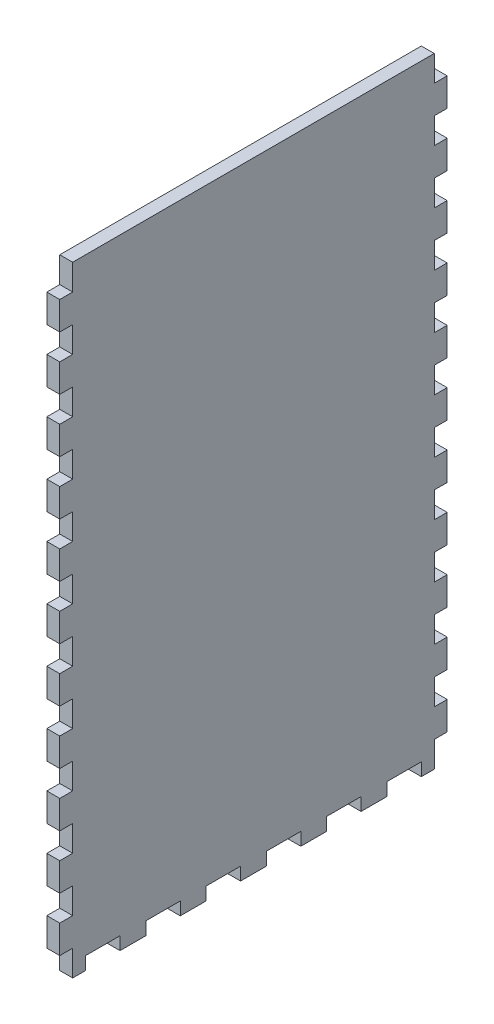
SolidWorks part; units mm, degrees
material "Acrylic (Medium-high impact)"
ref_plane "Front Plane" through (0, 0, 0) normal (0, 0, 1) x (1, 0, 0)
ref_plane "Top Plane" through (0, 0, 0) normal (0, 1, 0) x (1, 0, 0)
ref_plane "Right Plane" through (0, 0, 0) normal (1, 0, 0) x (0, 0, -1)
sketch "Sketch1" plane through (0, 0, 0) normal (0, 1, 0) x (1, 0, 0)
  line L1 (-254, 95.25) -> (254, 95.25)
  line L2 (-254, 95.25) -> (-254, -95.25)
  line L3 (-254, -95.25) -> (254, -95.25)
  line L4 (254, 95.25) -> (254, -95.25)
  point P4 (-254, 0)
  point P6 (0, 95.25)
  dimension "D1" = 190.5
  dimension "D2" = 508
extrude "Boss-Extrude1" add sketch "Sketch1" along normal blind 6.35
sketch "Sketch2" plane through (0, 6.35, 0) normal (0, 1, 0) x (1, 0, 0)
  line L0 (254, -95.25) -> (254, 95.25) construction
  line L1 (-254, 95.25) -> (254, 95.25)
  line L2 (-254, 95.25) -> (-254, -95.25)
  line L3 (-254, -95.25) -> (254, -95.25)
  line L4 (254, 95.25) -> (254, -95.25)
  line L5 (-254, -95.25) -> (254, -95.25) construction
  line L7 (-247.65, 88.9) -> (247.65, 88.9)
  line L8 (-247.65, 88.9) -> (-247.65, -88.9)
  line L9 (-247.65, -88.9) -> (247.65, -88.9)
  line L10 (247.65, 88.9) -> (247.65, -88.9)
  point P7 (-247.65, 0)
  point P14 (-254, 0)
  point P15 (0, -88.9)
  point P16 (0, -95.25)
  point P17 (247.65, 0)
  point P18 (254, 0)
  dimension "D1" = 6.35
  dimension "D2" = 6.35
extrude "Boss-Extrude2" add sketch "Sketch2" along normal blind 298.45
sketch "Sketch3" plane through (0, 0, 95.25) normal (0, 0, 1) x (1, 0, 0)
  line L0 (0, 304.8) -> (0, 0) construction
  line L1 (-254, 304.8) -> (254, 304.8) construction
  line L2 (-247.65, 6.35) -> (247.65, 6.35) construction
  line L4 (-3.302, 283.21) -> (-3.302, 6.35)
  line L5 (-3.302, 6.35) -> (3.302, 6.35)
  line L6 (3.302, 292.354) -> (3.302, 6.35)
  line L7 (3.302, 292.354) -> (-16.256, 292.354)
  line L9 (-5.842, 285.75) -> (-16.256, 285.75)
  line L10 (-16.256, 292.354) -> (-16.256, 285.75)
  line L11 (3.302, 101.6) -> (16.002, 101.6) construction
  line L12 (-254, 0) -> (254, 0) construction
  line L13 (12.827, 88.9) -> (12.827, 101.6) construction
  line L14 (9.652, 88.9) -> (16.002, 88.9)
  line L15 (9.652, 88.9) -> (9.652, 71.9667)
  line L16 (9.652, 71.9667) -> (16.002, 71.9667)
  line L17 (16.002, 88.9) -> (16.002, 71.9667)
  line L18 (9.652, 42.3333) -> (16.002, 42.3333)
  line L19 (9.652, 42.3333) -> (9.652, 59.2667)
  line L20 (9.652, 59.2667) -> (16.002, 59.2667)
  line L21 (16.002, 42.3333) -> (16.002, 59.2667)
  line L26 (9.652, 29.6333) -> (16.002, 29.6333)
  line L27 (9.652, 29.6333) -> (9.652, 12.7)
  line L28 (9.652, 12.7) -> (16.002, 12.7)
  line L29 (16.002, 29.6333) -> (16.002, 12.7)
  line L30 (12.827, 59.2667) -> (12.827, 71.9667) construction
  line L31 (12.827, 29.6333) -> (12.827, 42.3333) construction
  line L32 (12.827, 12.7) -> (12.827, 0) construction
  arc A0 (-3.302, 283.21) -> (-5.842, 285.75) centre (-5.842, 283.21) ccw
  point P5 (0, 6.35)
  dimension "D5" = 2.54
  dimension "D1" = 6.604
  dimension "D2" = 12.954
  dimension "D3" = 6.604
  dimension "D4" = 286.004
  dimension "D6" = 101.6
  dimension "D7" = 12.7
  dimension "D8" = 12.7
  dimension "D9" = 6.35
extrude "Cut-Extrude1" cut sketch "Sketch3" against normal blind 12.7
sketch "Sketch4" plane through (0, 0, -88.9) normal (0, 0, 1) x (1, 0, 0)
  line L0 (-254, 304.8) -> (254, 304.8) construction
  line L1 (-22.606, 304.8) -> (-16.256, 304.8)
  line L2 (-22.606, 304.8) -> (-22.606, 6.35)
  line L3 (-22.606, 6.35) -> (-16.256, 6.35)
  line L4 (-16.256, 304.8) -> (-16.256, 6.35)
  line L5 (6.477, 263.525) -> (6.477, 247.65) construction
  line L6 (-16.256, 292.354) -> (-16.256, 285.75) construction
  line L7 (3.302, 304.8) -> (9.652, 304.8)
  line L8 (3.302, 304.8) -> (3.302, 6.35)
  line L9 (3.302, 6.35) -> (9.652, 6.35)
  line L10 (9.652, 304.8) -> (9.652, 6.35)
  line L11 (247.65, 6.35) -> (-247.65, 6.35) construction
  line L12 (3.302, 6.35) -> (3.302, 292.354) construction
  line L13 (-16.256, 304.8) -> (-22.606, 304.8)
  line L14 (-16.256, 304.8) -> (-16.256, 292.1)
  line L15 (-16.256, 292.1) -> (-22.606, 292.1)
  line L16 (-22.606, 304.8) -> (-22.606, 292.1)
  line L17 (-16.256, 276.225) -> (-22.606, 276.225)
  line L18 (-16.256, 276.225) -> (-16.256, 263.525)
  line L19 (-16.256, 263.525) -> (-22.606, 263.525)
  line L20 (-22.606, 276.225) -> (-22.606, 263.525)
  line L21 (-22.606, 6.35) -> (-16.256, 6.35)
  line L22 (-22.606, 6.35) -> (-22.606, 19.05)
  line L23 (-22.606, 19.05) -> (-16.256, 19.05)
  line L24 (-16.256, 6.35) -> (-16.256, 19.05)
  line L25 (-22.606, 34.925) -> (-16.256, 34.925)
  line L26 (-22.606, 34.925) -> (-22.606, 47.625)
  line L27 (-22.606, 47.625) -> (-16.256, 47.625)
  line L28 (-16.256, 34.925) -> (-16.256, 47.625)
  line L29 (-22.606, 92.075) -> (-16.256, 92.075)
  line L30 (-22.606, 92.075) -> (-22.606, 104.775)
  line L31 (-22.606, 104.775) -> (-16.256, 104.775)
  line L32 (-16.256, 92.075) -> (-16.256, 104.775)
  line L33 (-22.606, 149.225) -> (-16.256, 149.225)
  line L34 (-22.606, 149.225) -> (-22.606, 161.925)
  line L35 (-22.606, 161.925) -> (-16.256, 161.925)
  line L36 (-16.256, 149.225) -> (-16.256, 161.925)
  line L37 (-22.606, 177.8) -> (-16.256, 177.8)
  line L38 (-22.606, 177.8) -> (-22.606, 190.5)
  line L39 (-22.606, 190.5) -> (-16.256, 190.5)
  line L40 (-16.256, 177.8) -> (-16.256, 190.5)
  line L41 (-22.606, 206.375) -> (-16.256, 206.375)
  line L42 (-22.606, 206.375) -> (-22.606, 219.075)
  line L43 (-22.606, 219.075) -> (-16.256, 219.075)
  line L44 (-16.256, 206.375) -> (-16.256, 219.075)
  line L45 (-22.606, 234.95) -> (-16.256, 234.95)
  line L46 (-22.606, 234.95) -> (-22.606, 247.65)
  line L47 (-22.606, 247.65) -> (-16.256, 247.65)
  line L48 (-16.256, 234.95) -> (-16.256, 247.65)
  line L49 (-16.256, 133.35) -> (-22.606, 133.35)
  line L50 (-16.256, 133.35) -> (-16.256, 120.65)
  line L51 (-16.256, 120.65) -> (-22.606, 120.65)
  line L52 (-22.606, 133.35) -> (-22.606, 120.65)
  line L53 (-16.256, 76.2) -> (-22.606, 76.2)
  line L54 (-16.256, 76.2) -> (-16.256, 63.5)
  line L55 (-16.256, 63.5) -> (-22.606, 63.5)
  line L56 (-22.606, 76.2) -> (-22.606, 63.5)
  line L57 (-19.431, 304.8) -> (-19.431, 292.1) construction
  line L58 (-19.431, 292.1) -> (-19.431, 276.225) construction
  line L59 (-19.431, 276.225) -> (-19.431, 263.525) construction
  line L60 (-19.431, 247.65) -> (-19.431, 234.95) construction
  line L61 (-19.431, 234.95) -> (-19.431, 219.075) construction
  line L62 (-19.431, 219.075) -> (-19.431, 206.375) construction
  line L63 (-19.431, 206.375) -> (-19.431, 190.5) construction
  line L64 (-19.431, 190.5) -> (-19.431, 177.8) construction
  line L65 (-19.431, 177.8) -> (-19.431, 161.925) construction
  line L66 (-19.431, 161.925) -> (-19.431, 149.225) construction
  line L67 (-19.431, 133.35) -> (-19.431, 120.65) construction
  line L68 (-19.431, 120.65) -> (-19.431, 104.775) construction
  line L69 (-19.431, 104.775) -> (-19.431, 92.075) construction
  line L70 (-19.431, 92.075) -> (-19.431, 76.2) construction
  line L71 (-19.431, 76.2) -> (-19.431, 63.5) construction
  line L72 (-19.431, 63.5) -> (-19.431, 47.625) construction
  line L73 (-19.431, 47.625) -> (-19.431, 34.925) construction
  line L74 (-19.431, 34.925) -> (-19.431, 19.05) construction
  line L75 (-19.431, 19.05) -> (-19.431, 6.35) construction
  line L76 (-19.431, 149.225) -> (-19.431, 133.35) construction
  line L77 (-19.431, 263.525) -> (-19.431, 247.65) construction
  line L78 (-6.477, 304.8) -> (-6.477, 0) construction
  line L79 (254, 304.8) -> (-254, 304.8) construction
  line L80 (254, 0) -> (-254, 0) construction
  line L81 (-6.477, 8.3493) -> (3.302, 8.3493) construction
  line L82 (-6.477, 8.3493) -> (-16.256, 8.3493) construction
  line L83 (6.477, 149.225) -> (6.477, 133.35) construction
  line L84 (6.477, 19.05) -> (6.477, 6.35) construction
  line L85 (6.477, 34.925) -> (6.477, 19.05) construction
  line L86 (6.477, 47.625) -> (6.477, 34.925) construction
  line L87 (6.477, 63.5) -> (6.477, 47.625) construction
  line L88 (6.477, 76.2) -> (6.477, 63.5) construction
  line L89 (6.477, 92.075) -> (6.477, 76.2) construction
  line L90 (6.477, 104.775) -> (6.477, 92.075) construction
  line L91 (6.477, 120.65) -> (6.477, 104.775) construction
  line L92 (6.477, 133.35) -> (6.477, 120.65) construction
  line L93 (6.477, 161.925) -> (6.477, 149.225) construction
  line L94 (6.477, 177.8) -> (6.477, 161.925) construction
  line L95 (6.477, 190.5) -> (6.477, 177.8) construction
  line L96 (6.477, 206.375) -> (6.477, 190.5) construction
  line L97 (6.477, 219.075) -> (6.477, 206.375) construction
  line L98 (6.477, 234.95) -> (6.477, 219.075) construction
  line L99 (6.477, 247.65) -> (6.477, 234.95) construction
  line L100 (6.477, 276.225) -> (6.477, 263.525) construction
  line L101 (6.477, 292.1) -> (6.477, 276.225) construction
  line L102 (6.477, 304.8) -> (6.477, 292.1) construction
  line L103 (9.652, 76.2) -> (9.652, 63.5)
  line L104 (3.302, 63.5) -> (9.652, 63.5)
  line L105 (3.302, 76.2) -> (3.302, 63.5)
  line L106 (3.302, 76.2) -> (9.652, 76.2)
  line L107 (9.652, 133.35) -> (9.652, 120.65)
  line L108 (3.302, 120.65) -> (9.652, 120.65)
  line L109 (3.302, 133.35) -> (3.302, 120.65)
  line L110 (3.302, 133.35) -> (9.652, 133.35)
  line L111 (3.302, 234.95) -> (3.302, 247.65)
  line L112 (9.652, 247.65) -> (3.302, 247.65)
  line L113 (9.652, 234.95) -> (9.652, 247.65)
  line L114 (9.652, 234.95) -> (3.302, 234.95)
  line L115 (3.302, 206.375) -> (3.302, 219.075)
  line L116 (9.652, 219.075) -> (3.302, 219.075)
  line L117 (9.652, 206.375) -> (9.652, 219.075)
  line L118 (9.652, 206.375) -> (3.302, 206.375)
  line L119 (3.302, 177.8) -> (3.302, 190.5)
  line L120 (9.652, 190.5) -> (3.302, 190.5)
  line L121 (9.652, 177.8) -> (9.652, 190.5)
  line L122 (9.652, 177.8) -> (3.302, 177.8)
  line L123 (3.302, 149.225) -> (3.302, 161.925)
  line L124 (9.652, 161.925) -> (3.302, 161.925)
  line L125 (9.652, 149.225) -> (9.652, 161.925)
  line L126 (9.652, 149.225) -> (3.302, 149.225)
  line L127 (3.302, 92.075) -> (3.302, 104.775)
  line L128 (9.652, 104.775) -> (3.302, 104.775)
  line L129 (9.652, 92.075) -> (9.652, 104.775)
  line L130 (9.652, 92.075) -> (3.302, 92.075)
  line L131 (3.302, 34.925) -> (3.302, 47.625)
  line L132 (9.652, 47.625) -> (3.302, 47.625)
  line L133 (9.652, 34.925) -> (9.652, 47.625)
  line L134 (9.652, 34.925) -> (3.302, 34.925)
  line L135 (3.302, 6.35) -> (3.302, 19.05)
  line L136 (9.652, 19.05) -> (3.302, 19.05)
  line L137 (9.652, 6.35) -> (9.652, 19.05)
  line L138 (9.652, 6.35) -> (3.302, 6.35)
  line L139 (9.652, 276.225) -> (9.652, 263.525)
  line L140 (3.302, 263.525) -> (9.652, 263.525)
  line L141 (3.302, 276.225) -> (3.302, 263.525)
  line L142 (3.302, 276.225) -> (9.652, 276.225)
  line L143 (9.652, 304.8) -> (9.652, 292.1)
  line L144 (3.302, 292.1) -> (9.652, 292.1)
  line L145 (3.302, 304.8) -> (3.302, 292.1)
  line L146 (3.302, 304.8) -> (9.652, 304.8)
  line L147 (3.302, 304.8) -> (3.302, 6.35)
  line L148 (9.652, 6.35) -> (3.302, 6.35)
  line L149 (9.652, 304.8) -> (9.652, 6.35)
  line L150 (9.652, 304.8) -> (3.302, 304.8)
  point P14 (-16.256, 289.052)
  dimension "D1" = 6.35
  dimension "D2" = 12.7
extrude "Cut-Extrude2" cut sketch "Sketch4" against normal up to next (6.35 mm away) contours L17 L4 L15 L2 | L2 L47 L4 L19 | L45 L2 L43 L4 | L41 L2 L39 L4 | L37 L2 L35 L4 | L49 L4 L33 L2 | L4 L51 L2 L31 | L53 L4 L29 L2 | L4 L55 L2 L27 | L25 L2 L23 L4
ref_plane "Plane1" through (-6.477, 0, 0) normal (-1, 0, 0) x (0, 0, 1)
mirror "Mirror1" about plane through (-6.477, 0, 0) normal (-1, 0, 0) of "Cut-Extrude2"
sketch "Sketch5" plane through (0, 0, 0) normal (0, -1, 0) x (-1, 0, 0)
  line L0 (-227.9316, -95.25) -> (-227.9316, -88.9)
  line L1 (-247.65, 88.9) -> (247.65, 88.9)
  line L2 (-247.65, 88.9) -> (-247.65, -88.9)
  line L3 (-247.65, -88.9) -> (247.65, -88.9)
  line L4 (247.65, 88.9) -> (247.65, -88.9)
  line L5 (-254, -95.25) -> (-241.3, -95.25)
  line L6 (-254, -95.25) -> (-254, -88.9)
  line L7 (-254, -88.9) -> (-241.3, -88.9)
  line L8 (-241.3, -95.25) -> (-241.3, -88.9)
  line L9 (-227.9316, -95.25) -> (-215.2316, -95.25)
  line L10 (-227.9316, -88.9) -> (-215.2316, -88.9)
  line L11 (-215.2316, -95.25) -> (-215.2316, -88.9)
  line L12 (-201.8632, -95.25) -> (-201.8632, -88.9)
  line L13 (-201.8632, -95.25) -> (-189.1632, -95.25)
  line L14 (-201.8632, -88.9) -> (-189.1632, -88.9)
  line L15 (-189.1632, -95.25) -> (-189.1632, -88.9)
  line L16 (-175.7947, -95.25) -> (-175.7947, -88.9)
  line L17 (-175.7947, -95.25) -> (-163.0947, -95.25)
  line L18 (-175.7947, -88.9) -> (-163.0947, -88.9)
  line L19 (-163.0947, -95.25) -> (-163.0947, -88.9)
  line L20 (-149.7263, -95.25) -> (-149.7263, -88.9)
  line L21 (-149.7263, -95.25) -> (-137.0263, -95.25)
  line L22 (-149.7263, -88.9) -> (-137.0263, -88.9)
  line L23 (-137.0263, -95.25) -> (-137.0263, -88.9)
  line L24 (-123.6579, -95.25) -> (-123.6579, -88.9)
  line L25 (-123.6579, -95.25) -> (-110.9579, -95.25)
  line L26 (-123.6579, -88.9) -> (-110.9579, -88.9)
  line L27 (-110.9579, -95.25) -> (-110.9579, -88.9)
  line L28 (-97.5895, -95.25) -> (-97.5895, -88.9)
  line L29 (-97.5895, -95.25) -> (-84.8895, -95.25)
  line L30 (-97.5895, -88.9) -> (-84.8895, -88.9)
  line L31 (-84.8895, -95.25) -> (-84.8895, -88.9)
  line L32 (-71.5211, -95.25) -> (-71.5211, -88.9)
  line L33 (-71.5211, -95.25) -> (-58.8211, -95.25)
  line L34 (-71.5211, -88.9) -> (-58.8211, -88.9)
  line L35 (-58.8211, -95.25) -> (-58.8211, -88.9)
  line L36 (-45.4526, -95.25) -> (-45.4526, -88.9)
  line L37 (-45.4526, -95.25) -> (-32.7526, -95.25)
  line L38 (-45.4526, -88.9) -> (-32.7526, -88.9)
  line L39 (-32.7526, -95.25) -> (-32.7526, -88.9)
  line L40 (-19.3842, -95.25) -> (-19.3842, -88.9)
  line L41 (-19.3842, -95.25) -> (-6.6842, -95.25)
  line L42 (-19.3842, -88.9) -> (-6.6842, -88.9)
  line L43 (-6.6842, -95.25) -> (-6.6842, -88.9)
  line L44 (6.6842, -95.25) -> (6.6842, -88.9)
  line L45 (6.6842, -95.25) -> (19.3842, -95.25)
  line L46 (6.6842, -88.9) -> (19.3842, -88.9)
  line L47 (19.3842, -95.25) -> (19.3842, -88.9)
  line L48 (32.7526, -95.25) -> (32.7526, -88.9)
  line L49 (32.7526, -95.25) -> (45.4526, -95.25)
  line L50 (32.7526, -88.9) -> (45.4526, -88.9)
  line L51 (45.4526, -95.25) -> (45.4526, -88.9)
  line L52 (58.8211, -95.25) -> (58.8211, -88.9)
  line L53 (58.8211, -95.25) -> (71.5211, -95.25)
  line L54 (58.8211, -88.9) -> (71.5211, -88.9)
  line L55 (71.5211, -95.25) -> (71.5211, -88.9)
  line L56 (84.8895, -95.25) -> (84.8895, -88.9)
  line L57 (84.8895, -95.25) -> (97.5895, -95.25)
  line L58 (84.8895, -88.9) -> (97.5895, -88.9)
  line L59 (97.5895, -95.25) -> (97.5895, -88.9)
  line L60 (110.9579, -95.25) -> (110.9579, -88.9)
  line L61 (110.9579, -95.25) -> (123.6579, -95.25)
  line L62 (110.9579, -88.9) -> (123.6579, -88.9)
  line L63 (123.6579, -95.25) -> (123.6579, -88.9)
  line L64 (137.0263, -95.25) -> (137.0263, -88.9)
  line L65 (137.0263, -95.25) -> (149.7263, -95.25)
  line L66 (137.0263, -88.9) -> (149.7263, -88.9)
  line L67 (149.7263, -95.25) -> (149.7263, -88.9)
  line L68 (163.0947, -95.25) -> (163.0947, -88.9)
  line L69 (163.0947, -95.25) -> (175.7947, -95.25)
  line L70 (163.0947, -88.9) -> (175.7947, -88.9)
  line L71 (175.7947, -95.25) -> (175.7947, -88.9)
  line L72 (189.1632, -95.25) -> (189.1632, -88.9)
  line L73 (189.1632, -95.25) -> (201.8632, -95.25)
  line L74 (189.1632, -88.9) -> (201.8632, -88.9)
  line L75 (201.8632, -95.25) -> (201.8632, -88.9)
  line L76 (215.2316, -95.25) -> (215.2316, -88.9)
  line L77 (215.2316, -95.25) -> (227.9316, -95.25)
  line L78 (215.2316, -88.9) -> (227.9316, -88.9)
  line L79 (227.9316, -95.25) -> (227.9316, -88.9)
  line L80 (241.3, -95.25) -> (241.3, -88.9)
  line L81 (241.3, -95.25) -> (254, -95.25)
  line L82 (241.3, -88.9) -> (254, -88.9)
  line L83 (254, -95.25) -> (254, -88.9)
  line L84 (-167.64, 0) -> (167.64, 0) construction
  line L85 (254, 95.25) -> (254, 88.9)
  line L86 (241.3, 88.9) -> (254, 88.9)
  line L87 (241.3, 95.25) -> (254, 95.25)
  line L88 (241.3, 95.25) -> (241.3, 88.9)
  line L89 (227.9316, 95.25) -> (227.9316, 88.9)
  line L90 (215.2316, 88.9) -> (227.9316, 88.9)
  line L91 (215.2316, 95.25) -> (227.9316, 95.25)
  line L92 (215.2316, 95.25) -> (215.2316, 88.9)
  line L93 (201.8632, 95.25) -> (201.8632, 88.9)
  line L94 (189.1632, 88.9) -> (201.8632, 88.9)
  line L95 (189.1632, 95.25) -> (201.8632, 95.25)
  line L96 (189.1632, 95.25) -> (189.1632, 88.9)
  line L97 (175.7947, 95.25) -> (175.7947, 88.9)
  line L98 (163.0947, 88.9) -> (175.7947, 88.9)
  line L99 (163.0947, 95.25) -> (175.7947, 95.25)
  line L100 (163.0947, 95.25) -> (163.0947, 88.9)
  line L101 (149.7263, 95.25) -> (149.7263, 88.9)
  line L102 (137.0263, 88.9) -> (149.7263, 88.9)
  line L103 (137.0263, 95.25) -> (149.7263, 95.25)
  line L104 (137.0263, 95.25) -> (137.0263, 88.9)
  line L105 (123.6579, 95.25) -> (123.6579, 88.9)
  line L106 (110.9579, 88.9) -> (123.6579, 88.9)
  line L107 (110.9579, 95.25) -> (123.6579, 95.25)
  line L108 (110.9579, 95.25) -> (110.9579, 88.9)
  line L109 (97.5895, 95.25) -> (97.5895, 88.9)
  line L110 (84.8895, 88.9) -> (97.5895, 88.9)
  line L111 (84.8895, 95.25) -> (97.5895, 95.25)
  line L112 (84.8895, 95.25) -> (84.8895, 88.9)
  line L113 (71.5211, 95.25) -> (71.5211, 88.9)
  line L114 (58.8211, 88.9) -> (71.5211, 88.9)
  line L115 (58.8211, 95.25) -> (71.5211, 95.25)
  line L116 (58.8211, 95.25) -> (58.8211, 88.9)
  line L117 (45.4526, 95.25) -> (45.4526, 88.9)
  line L118 (32.7526, 88.9) -> (45.4526, 88.9)
  line L119 (32.7526, 95.25) -> (45.4526, 95.25)
  line L120 (32.7526, 95.25) -> (32.7526, 88.9)
  line L121 (19.3842, 95.25) -> (19.3842, 88.9)
  line L122 (6.6842, 88.9) -> (19.3842, 88.9)
  line L123 (6.6842, 95.25) -> (19.3842, 95.25)
  line L124 (6.6842, 95.25) -> (6.6842, 88.9)
  line L125 (-6.6842, 95.25) -> (-6.6842, 88.9)
  line L126 (-19.3842, 88.9) -> (-6.6842, 88.9)
  line L127 (-19.3842, 95.25) -> (-6.6842, 95.25)
  line L128 (-19.3842, 95.25) -> (-19.3842, 88.9)
  line L129 (-32.7526, 95.25) -> (-32.7526, 88.9)
  line L130 (-45.4526, 88.9) -> (-32.7526, 88.9)
  line L131 (-45.4526, 95.25) -> (-32.7526, 95.25)
  line L132 (-45.4526, 95.25) -> (-45.4526, 88.9)
  line L133 (-58.8211, 95.25) -> (-58.8211, 88.9)
  line L134 (-71.5211, 88.9) -> (-58.8211, 88.9)
  line L135 (-71.5211, 95.25) -> (-58.8211, 95.25)
  line L136 (-71.5211, 95.25) -> (-71.5211, 88.9)
  line L137 (-84.8895, 95.25) -> (-84.8895, 88.9)
  line L138 (-97.5895, 88.9) -> (-84.8895, 88.9)
  line L139 (-97.5895, 95.25) -> (-84.8895, 95.25)
  line L140 (-97.5895, 95.25) -> (-97.5895, 88.9)
  line L141 (-110.9579, 95.25) -> (-110.9579, 88.9)
  line L142 (-123.6579, 88.9) -> (-110.9579, 88.9)
  line L143 (-123.6579, 95.25) -> (-110.9579, 95.25)
  line L144 (-123.6579, 95.25) -> (-123.6579, 88.9)
  line L145 (-137.0263, 95.25) -> (-137.0263, 88.9)
  line L146 (-149.7263, 88.9) -> (-137.0263, 88.9)
  line L147 (-149.7263, 95.25) -> (-137.0263, 95.25)
  line L148 (-149.7263, 95.25) -> (-149.7263, 88.9)
  line L149 (-163.0947, 95.25) -> (-163.0947, 88.9)
  line L150 (-175.7947, 88.9) -> (-163.0947, 88.9)
  line L151 (-175.7947, 95.25) -> (-163.0947, 95.25)
  line L152 (-175.7947, 95.25) -> (-175.7947, 88.9)
  line L153 (-189.1632, 95.25) -> (-189.1632, 88.9)
  line L154 (-201.8632, 88.9) -> (-189.1632, 88.9)
  line L155 (-201.8632, 95.25) -> (-189.1632, 95.25)
  line L156 (-201.8632, 95.25) -> (-201.8632, 88.9)
  line L157 (-215.2316, 95.25) -> (-215.2316, 88.9)
  line L158 (-227.9316, 88.9) -> (-215.2316, 88.9)
  line L159 (-227.9316, 95.25) -> (-215.2316, 95.25)
  line L160 (-241.3, 95.25) -> (-241.3, 88.9)
  line L161 (-254, 88.9) -> (-241.3, 88.9)
  line L162 (-254, 95.25) -> (-254, 88.9)
  line L163 (-254, 95.25) -> (-241.3, 95.25)
  line L164 (-247.65, 88.9) -> (247.65, 88.9)
  line L165 (-227.9316, 95.25) -> (-227.9316, 88.9)
  line L166 (-254, 65.6167) -> (-254, 52.9167)
  line L167 (-254, 95.25) -> (-247.65, 95.25)
  line L168 (-254, 95.25) -> (-254, 82.55)
  line L169 (-254, 82.55) -> (-247.65, 82.55)
  line L170 (-247.65, 95.25) -> (-247.65, 82.55)
  line L171 (-254, 65.6167) -> (-247.65, 65.6167)
  line L172 (-247.65, 65.6167) -> (-247.65, 52.9167)
  line L173 (-254, 52.9167) -> (-247.65, 52.9167)
  line L174 (-254, 35.9833) -> (-254, 23.2833)
  line L175 (-254, 35.9833) -> (-247.65, 35.9833)
  line L176 (-247.65, 35.9833) -> (-247.65, 23.2833)
  line L177 (-254, 23.2833) -> (-247.65, 23.2833)
  line L178 (-254, 6.35) -> (-254, -6.35)
  line L179 (-254, 6.35) -> (-247.65, 6.35)
  line L180 (-247.65, 6.35) -> (-247.65, -6.35)
  line L181 (-254, -6.35) -> (-247.65, -6.35)
  line L182 (-254, -23.2833) -> (-254, -35.9833)
  line L183 (-254, -23.2833) -> (-247.65, -23.2833)
  line L184 (-247.65, -23.2833) -> (-247.65, -35.9833)
  line L185 (-254, -35.9833) -> (-247.65, -35.9833)
  line L186 (-254, -52.9167) -> (-254, -65.6167)
  line L187 (-254, -52.9167) -> (-247.65, -52.9167)
  line L188 (-247.65, -52.9167) -> (-247.65, -65.6167)
  line L189 (-254, -65.6167) -> (-247.65, -65.6167)
  line L190 (-254, -82.55) -> (-254, -95.25)
  line L191 (-254, -82.55) -> (-247.65, -82.55)
  line L192 (-247.65, -82.55) -> (-247.65, -95.25)
  line L193 (-254, -95.25) -> (-247.65, -95.25)
  line L194 (0, 104.775) -> (0, -104.775) construction
  line L195 (254, -95.25) -> (247.65, -95.25)
  line L196 (247.65, -82.55) -> (247.65, -95.25)
  line L197 (254, -82.55) -> (247.65, -82.55)
  line L198 (254, -82.55) -> (254, -95.25)
  line L199 (254, -65.6167) -> (247.65, -65.6167)
  line L200 (247.65, -52.9167) -> (247.65, -65.6167)
  line L201 (254, -52.9167) -> (247.65, -52.9167)
  line L202 (254, -52.9167) -> (254, -65.6167)
  line L203 (254, -35.9833) -> (247.65, -35.9833)
  line L204 (247.65, -23.2833) -> (247.65, -35.9833)
  line L205 (254, -23.2833) -> (247.65, -23.2833)
  line L206 (254, -23.2833) -> (254, -35.9833)
  line L207 (254, -6.35) -> (247.65, -6.35)
  line L208 (247.65, 6.35) -> (247.65, -6.35)
  line L209 (254, 6.35) -> (247.65, 6.35)
  line L210 (254, 6.35) -> (254, -6.35)
  line L211 (254, 23.2833) -> (247.65, 23.2833)
  line L212 (247.65, 35.9833) -> (247.65, 23.2833)
  line L213 (254, 35.9833) -> (247.65, 35.9833)
  line L214 (254, 35.9833) -> (254, 23.2833)
  line L215 (254, 52.9167) -> (247.65, 52.9167)
  line L216 (247.65, 65.6167) -> (247.65, 52.9167)
  line L217 (254, 65.6167) -> (247.65, 65.6167)
  line L218 (247.65, 95.25) -> (247.65, 82.55)
  line L219 (254, 82.55) -> (247.65, 82.55)
  line L220 (254, 95.25) -> (254, 82.55)
  line L221 (254, 95.25) -> (247.65, 95.25)
  line L222 (254, 65.6167) -> (254, 52.9167)
  line L223 (254, 95.25) -> (254, 88.9)
  line L224 (254, -95.25) -> (254, -88.9)
  line L225 (247.65, 88.9) -> (247.65, -88.9)
  line M114 (254, -95.25) -> (254, 95.25)
  dimension "D1" = 12.7
  dimension "D3" = 6.35
  dimension "D5" = 12.7
  dimension "D2" = 20
  dimension "D4" = 7
sketch "Sketch6" plane through (0, 0, 0) normal (0, 1, 0) x (1, 0, 0)
  line L1 (-247.65, 117.4399) -> (267.1511, 117.4399)
  line L2 (-247.65, 117.4399) -> (-247.65, -137.4416)
  line L3 (-247.65, -137.4416) -> (267.1511, -137.4416)
  line L4 (267.1511, 117.4399) -> (267.1511, -137.4416)
  line L6 (-247.65, 88.9) -> (-247.65, -88.9) construction
  point P4 (-247.65, 144.2667)
  point P5 (-247.65, -168.1175)
extrude "Cut-Extrude5" cut sketch "Sketch6" along normal through all
extrude "Cut-Extrude6" cut sketch "Sketch5" against normal blind 6.35 contours L199 L4 L197 M114 | L203 L4 L201 M114 | L207 L4 L205 M114 | L211 L4 L209 M114 | L215 L4 L213 M114 | L219 L4 L217 M114
sketch "Sketch7" plane through (-254, 0, 0) normal (-1, 0, 0) x (0, 0, 1)
  line L0 (-95.25, 26.5545) -> (-95.25, 39.2545)
  line L1 (-95.25, 0) -> (-88.9, 0)
  line L2 (-95.25, 0) -> (-95.25, 12.7)
  line L3 (-95.25, 12.7) -> (-88.9, 12.7)
  line L4 (-88.9, 0) -> (-88.9, 12.7)
  line L5 (-95.25, 39.2545) -> (-88.9, 39.2545)
  line L6 (-88.9, 26.5545) -> (-88.9, 39.2545)
  line L7 (-95.25, 26.5545) -> (-88.9, 26.5545)
  line L8 (-95.25, 53.1091) -> (-95.25, 65.8091)
  line L9 (-95.25, 65.8091) -> (-88.9, 65.8091)
  line L10 (-88.9, 53.1091) -> (-88.9, 65.8091)
  line L11 (-95.25, 53.1091) -> (-88.9, 53.1091)
  line L12 (-95.25, 79.6636) -> (-95.25, 92.3636)
  line L13 (-95.25, 92.3636) -> (-88.9, 92.3636)
  line L14 (-88.9, 79.6636) -> (-88.9, 92.3636)
  line L15 (-95.25, 79.6636) -> (-88.9, 79.6636)
  line L16 (-95.25, 106.2182) -> (-95.25, 118.9182)
  line L17 (-95.25, 118.9182) -> (-88.9, 118.9182)
  line L18 (-88.9, 106.2182) -> (-88.9, 118.9182)
  line L19 (-95.25, 106.2182) -> (-88.9, 106.2182)
  line L20 (-95.25, 132.7727) -> (-95.25, 145.4727)
  line L21 (-95.25, 145.4727) -> (-88.9, 145.4727)
  line L22 (-88.9, 132.7727) -> (-88.9, 145.4727)
  line L23 (-95.25, 132.7727) -> (-88.9, 132.7727)
  line L24 (-95.25, 159.3273) -> (-95.25, 172.0273)
  line L25 (-95.25, 172.0273) -> (-88.9, 172.0273)
  line L26 (-88.9, 159.3273) -> (-88.9, 172.0273)
  line L27 (-95.25, 159.3273) -> (-88.9, 159.3273)
  line L28 (-95.25, 185.8818) -> (-95.25, 198.5818)
  line L29 (-95.25, 198.5818) -> (-88.9, 198.5818)
  line L30 (-88.9, 185.8818) -> (-88.9, 198.5818)
  line L31 (-95.25, 185.8818) -> (-88.9, 185.8818)
  line L32 (-95.25, 212.4364) -> (-95.25, 225.1364)
  line L33 (-95.25, 225.1364) -> (-88.9, 225.1364)
  line L34 (-88.9, 212.4364) -> (-88.9, 225.1364)
  line L35 (-95.25, 212.4364) -> (-88.9, 212.4364)
  line L36 (-95.25, 238.9909) -> (-95.25, 251.6909)
  line L37 (-95.25, 251.6909) -> (-88.9, 251.6909)
  line L38 (-88.9, 238.9909) -> (-88.9, 251.6909)
  line L39 (-95.25, 238.9909) -> (-88.9, 238.9909)
  line L40 (-95.25, 265.5455) -> (-95.25, 278.2455)
  line L41 (-95.25, 278.2455) -> (-88.9, 278.2455)
  line L42 (-88.9, 265.5455) -> (-88.9, 278.2455)
  line L43 (-95.25, 265.5455) -> (-88.9, 265.5455)
  line L44 (-95.25, 292.1) -> (-95.25, 304.8)
  line L45 (-95.25, 304.8) -> (-88.9, 304.8)
  line L46 (-88.9, 292.1) -> (-88.9, 304.8)
  line L47 (-95.25, 292.1) -> (-88.9, 292.1)
  line L48 (0, -3.4925) -> (0, 3.4925) construction
  line L49 (95.25, 292.1) -> (88.9, 292.1)
  line L50 (88.9, 292.1) -> (88.9, 304.8)
  line L51 (95.25, 304.8) -> (88.9, 304.8)
  line L52 (95.25, 292.1) -> (95.25, 304.8)
  line L53 (95.25, 265.5455) -> (88.9, 265.5455)
  line L54 (88.9, 265.5455) -> (88.9, 278.2455)
  line L55 (95.25, 278.2455) -> (88.9, 278.2455)
  line L56 (95.25, 265.5455) -> (95.25, 278.2455)
  line L57 (95.25, 238.9909) -> (88.9, 238.9909)
  line L58 (88.9, 238.9909) -> (88.9, 251.6909)
  line L59 (95.25, 251.6909) -> (88.9, 251.6909)
  line L60 (95.25, 238.9909) -> (95.25, 251.6909)
  line L61 (95.25, 212.4364) -> (88.9, 212.4364)
  line L62 (88.9, 212.4364) -> (88.9, 225.1364)
  line L63 (95.25, 225.1364) -> (88.9, 225.1364)
  line L64 (95.25, 212.4364) -> (95.25, 225.1364)
  line L65 (95.25, 185.8818) -> (88.9, 185.8818)
  line L66 (88.9, 185.8818) -> (88.9, 198.5818)
  line L67 (95.25, 198.5818) -> (88.9, 198.5818)
  line L68 (95.25, 185.8818) -> (95.25, 198.5818)
  line L69 (95.25, 159.3273) -> (88.9, 159.3273)
  line L70 (88.9, 159.3273) -> (88.9, 172.0273)
  line L71 (95.25, 172.0273) -> (88.9, 172.0273)
  line L72 (95.25, 159.3273) -> (95.25, 172.0273)
  line L73 (95.25, 132.7727) -> (88.9, 132.7727)
  line L74 (88.9, 132.7727) -> (88.9, 145.4727)
  line L75 (95.25, 145.4727) -> (88.9, 145.4727)
  line L76 (95.25, 132.7727) -> (95.25, 145.4727)
  line L77 (95.25, 106.2182) -> (88.9, 106.2182)
  line L78 (88.9, 106.2182) -> (88.9, 118.9182)
  line L79 (95.25, 118.9182) -> (88.9, 118.9182)
  line L80 (95.25, 106.2182) -> (95.25, 118.9182)
  line L81 (95.25, 79.6636) -> (88.9, 79.6636)
  line L82 (88.9, 79.6636) -> (88.9, 92.3636)
  line L83 (95.25, 92.3636) -> (88.9, 92.3636)
  line L84 (95.25, 79.6636) -> (95.25, 92.3636)
  line L85 (95.25, 53.1091) -> (88.9, 53.1091)
  line L86 (88.9, 53.1091) -> (88.9, 65.8091)
  line L87 (95.25, 65.8091) -> (88.9, 65.8091)
  line L88 (95.25, 53.1091) -> (95.25, 65.8091)
  line L89 (95.25, 26.5545) -> (88.9, 26.5545)
  line L90 (88.9, 26.5545) -> (88.9, 39.2545)
  line L91 (95.25, 39.2545) -> (88.9, 39.2545)
  line L92 (88.9, 0) -> (88.9, 12.7)
  line L93 (95.25, 12.7) -> (88.9, 12.7)
  line L94 (95.25, 0) -> (95.25, 12.7)
  line L95 (95.25, 0) -> (88.9, 0)
  line L96 (95.25, 26.5545) -> (95.25, 39.2545)
  point P5 (0, 0)
  point P6 (0, 0)
  dimension "D1" = 12.7
  dimension "D2" = 6.35
  dimension "D3" = 12
extrude "Cut-Extrude7" cut sketch "Sketch7" against normal through all
